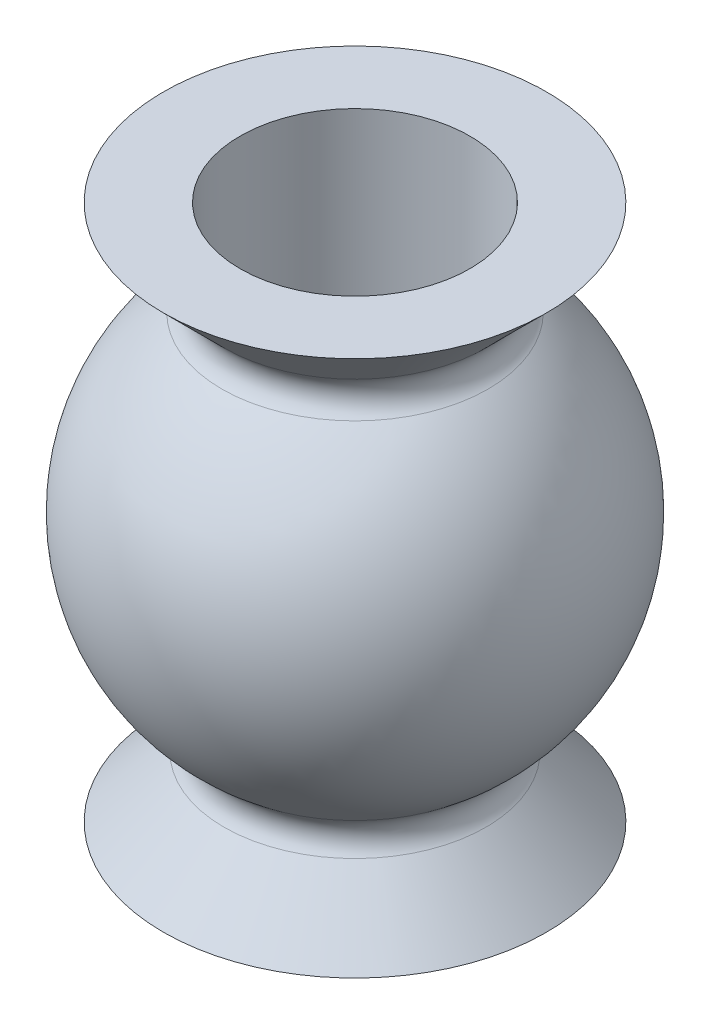
SolidWorks part; units mm, degrees
material "6063-O"
ref_plane "Front" through (0, 0, 0) normal (0, 0, 1) x (1, 0, 0)
ref_plane "Top" through (0, 0, 0) normal (0, 1, 0) x (1, 0, 0)
ref_plane "Right" through (0, 0, 0) normal (1, 0, 0) x (0, 0, -1)
sketch "Эскиз1" plane through (0, 0, 0) normal (1, 0, 0) x (0, 0, -1)
  line L8 (0, 0) -> (0, 3.5)
  line L13 (0, 3.5) -> (2.5, 3.5)
  line L14 (2.5, 3.5) -> (1.7087, 2.7087)
  line L15 (0, 0) -> (0, -3.5)
  line L16 (0, -3.5) -> (2.5, -3.5)
  line L17 (2.5, -3.5) -> (1.7087, -2.7087)
  line L18 (1.5, 3.5) -> (1.5, -3.5)
  arc A1 (1.7379, -2.2588) -> (1.7379, 2.2588) centre (0, 0) ccw
  arc A2 (0, 2.85) -> (0, -2.85) centre (0, 0) ccw
  arc A3 (1.7087, 2.7087) -> (1.7379, 2.2588) centre (1.9208, 2.4966) ccw
  arc A4 (1.7379, -2.2588) -> (1.7087, -2.7087) centre (1.9208, -2.4966) ccw
  dimension "D8" = 45
  dimension "D9" = 0.3
  dimension "D3" = 5.7
  dimension "D10" = 0.3
  dimension "D1" = 3.5
  dimension "D2" = 3.5
  dimension "D4" = 2.5
  dimension "D5" = 2.5
  dimension "D6" = 1.5
  dimension "D7" = 45
revolve "Повернуть1" add sketch "Эскиз1" angle 360 about L15
